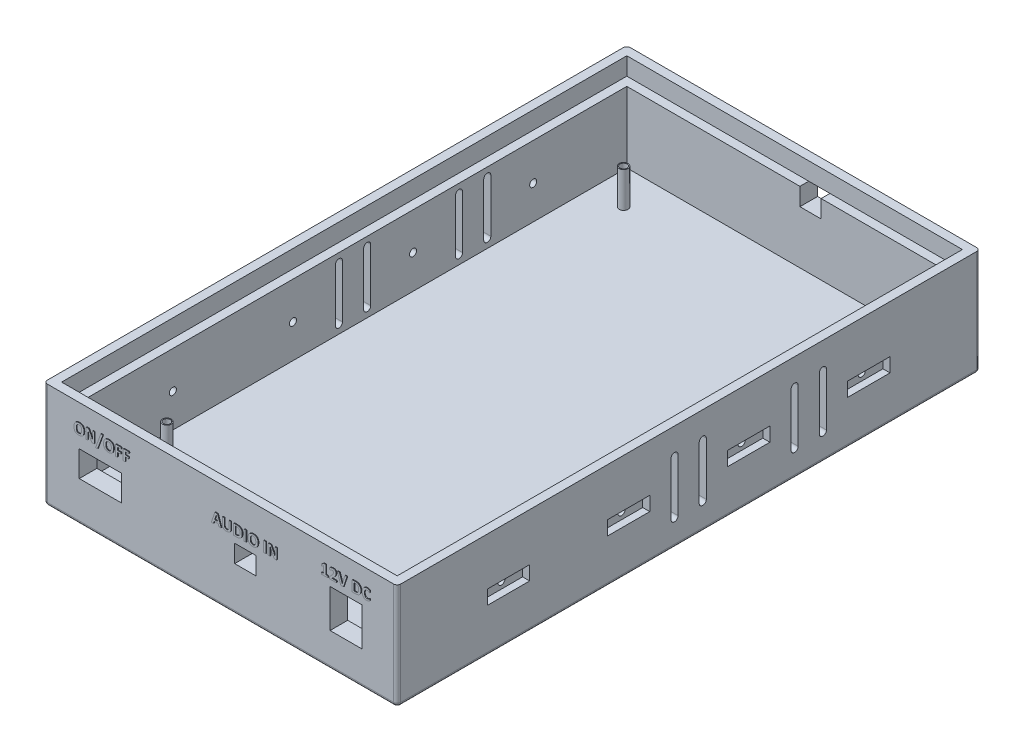
SolidWorks part; units mm, degrees
ref_plane "Front Plane" through (0, 0, 0) normal (0, 0, 1) x (1, 0, 0)
ref_plane "Top Plane" through (0, 0, 0) normal (0, 1, 0) x (1, 0, 0)
ref_plane "Right Plane" through (0, 0, 0) normal (1, 0, 0) x (0, 0, -1)
sketch "Sketch1" plane through (0, 0, 0) normal (0, 1, 0) x (1, 0, 0)
  line L1 (0, 0) -> (100, 0)
  line L2 (0, 0) -> (0, 165)
  line L3 (0, 165) -> (100, 165)
  line L4 (100, 0) -> (100, 165)
  dimension "D1" = 100
  dimension "D2" = 165
extrude "Boss-Extrude1" add sketch "Sketch1" along normal blind 30
sketch "Sketch2" plane through (0, 30, 0) normal (0, 1, 0) x (1, 0, 0)
  line L8 (5, 160) -> (5, 5)
  line L9 (5, 5) -> (95, 5)
  line L10 (95, 5) -> (95, 160)
  line L11 (95, 160) -> (5, 160)
  line L12 (5, 160) -> (5, 5)
  line L13 (5, 5) -> (95, 5)
  line L14 (95, 5) -> (95, 160)
  line L15 (95, 160) -> (5, 160)
  dimension "D1" = 5
extrude "Cut-Extrude1" cut sketch "Sketch2" against normal offset from surface (25 mm away) 5 up to face at (50, 0, -82.5)
sketch "Sketch3" plane through (0, 0, 0) normal (-1, 0, 0) x (0, 0, 1)
  line L1 (-126.3853, 10.954) -> (-116.3853, 10.954)
  line L2 (-126.3853, 10.954) -> (-126.3853, 5.954)
  line L3 (-126.3853, 5.954) -> (-116.3853, 5.954)
  line L4 (-116.3853, 10.954) -> (-116.3853, 5.954)
  dimension "D1" = 10
  dimension "D2" = 5
extrude "Boss-Extrude2" add sketch "Sketch3" along normal blind 15 separate body
sketch "Sketch4" plane through (0, 5.954, 0) normal (0, -1, 0) x (1, 0, 0)
  line L0 (-15, -116.3853) -> (0, -116.3853) construction
  line L1 (-15, -126.3853) -> (-10, -126.3853)
  line L2 (-15, -126.3853) -> (-15, -116.3853)
  line L3 (-15, -116.3853) -> (-10, -116.3853)
  line L4 (-10, -126.3853) -> (-10, -116.3853)
  dimension "D1" = 5
extrude "Boss-Extrude3" add sketch "Sketch4" along normal blind 20
chamfer "Chamfer1" distance 5 angle 45 1 edges at (-15, 10.954, -121.3853)
delete or keep bodies "Body-Delete/Keep 1" type delete bodies bodies 104
ref_plane "Plane1" through (50, 0, 0) normal (-1, 0, 0) x (0, 0, 1)
sketch "Sketch7" plane through (0, 0, 0) normal (-1, 0, 0) x (0, 0, 1)
  line L0 (-165, 30) -> (-165, 0) construction
  line L1 (-139.5, 16.5) -> (-127.5, 16.5)
  line L2 (-139.5, 16.5) -> (-139.5, 12.5)
  line L3 (-139.5, 12.5) -> (-127.5, 12.5)
  line L4 (-127.5, 16.5) -> (-127.5, 12.5)
  line L6 (-105.5, 16.5) -> (-105.5, 12.5)
  line L7 (-105.5, 16.5) -> (-93.5, 16.5)
  line L8 (-93.5, 16.5) -> (-93.5, 12.5)
  line L9 (-105.5, 12.5) -> (-93.5, 12.5)
  line L10 (-71.5, 16.5) -> (-71.5, 12.5)
  line L11 (-71.5, 16.5) -> (-59.5, 16.5)
  line L12 (-59.5, 16.5) -> (-59.5, 12.5)
  line L13 (-71.5, 12.5) -> (-59.5, 12.5)
  line L14 (-37.5, 16.5) -> (-37.5, 12.5)
  line L15 (-37.5, 16.5) -> (-25.5, 16.5)
  line L16 (-25.5, 16.5) -> (-25.5, 12.5)
  line L17 (-37.5, 12.5) -> (-25.5, 12.5)
  line L18 (0, 30) -> (0, 0) construction
  line L19 (-165, 0) -> (0, 0) construction
  dimension "D1" = 12
  dimension "D2" = 4
  dimension "D3" = 25.5
  dimension "D4" = 12.5
  dimension "D6" = 22
  dimension "D7" = 25.5
  dimension "D5" = 4
extrude "Cut-Extrude2" cut sketch "Sketch7" against normal blind 2
mirror "Mirror1" about plane through (50, 0, 0) normal (-1, 0, 0) of "Cut-Extrude2"
sketch "Sketch8" plane through (2, 0, 0) normal (-1, 0, 0) x (0, 0, 1)
  line L0 (-127.5, 12.5) -> (-127.5, 16.5) construction
  line L1 (-165, 30) -> (-165, 0) construction
  line L2 (-127.5, 16.5) -> (-139.5, 16.5) construction
  line L3 (0, 30) -> (0, 0) construction
  circle A0 centre (-133.5, 14.5) radius 1
  circle A1 centre (-99.5, 14.5) radius 1
  circle A2 centre (-65.5, 14.5) radius 1
  circle A3 centre (-31.5, 14.5) radius 1
  point P11 (-127.5, 14.5)
  point P17 (-133.5, 16.5)
  dimension "D1" = 2
  dimension "D2" = 2
  dimension "D3" = 2
  dimension "D4" = 2
  dimension "D5" = 34
  dimension "D8" = 31.5
  dimension "D9" = 31.5
  dimension "D6" = 34
  dimension "D7" = 34
extrude "Cut-Extrude3" cut sketch "Sketch8" against normal through all both and the other way through all
sketch "Sketch10" plane through (0, 0, 0) normal (0, 0, 1) x (1, 0, 0)
  line L0 (0, 30) -> (0, 0) construction
  line L1 (10, 18.65) -> (22, 18.65)
  line L2 (10, 18.65) -> (10, 11.35)
  line L3 (10, 11.35) -> (22, 11.35)
  line L4 (22, 18.65) -> (22, 11.35)
  point P4 (10, 15)
  point P7 (0, 15)
  dimension "D1" = 12
  dimension "D2" = 7.3
  dimension "D3" = 10
extrude "Cut-Extrude4" cut sketch "Sketch10" against normal up to surface (5 mm away) up to face at (50, 17.5, -5)
sketch "Sketch11" plane through (0, 0, 0) normal (0, 0, 1) x (1, 0, 0)
  line L0 (100, 30) -> (100, 0) construction
  line L5 (54, 17.5) -> (60, 17.5)
  line L6 (54, 17.5) -> (54, 12.5)
  line L7 (54, 12.5) -> (60, 12.5)
  line L8 (60, 17.5) -> (60, 12.5)
  point P4 (54, 15)
  point P7 (100, 15)
  dimension "D1" = 6
  dimension "D2" = 5
  dimension "D3" = 40
extrude "Cut-Extrude5" cut sketch "Sketch11" against normal up to surface (5 mm away) up to face at (16, 15, -5)
sketch "Sketch12" plane through (0, 0, 0) normal (0, 0, 1) x (1, 0, 0)
  line L0 (100, 30) -> (100, 0) construction
  line L1 (81, 20.4) -> (90, 20.4)
  line L2 (81, 20.4) -> (81, 9.6)
  line L3 (81, 9.6) -> (90, 9.6)
  line L4 (90, 20.4) -> (90, 9.6)
  point P4 (90, 15)
  point P7 (100, 15)
  dimension "D1" = 10.8
  dimension "D2" = 9
  dimension "D3" = 10
extrude "Cut-Extrude6" cut sketch "Sketch12" against normal up to surface (5 mm away) up to face at (57, 15, -5)
sketch "Sketch13" plane through (0, 0, -165) normal (0, 0, -1) x (-1, 0, 0)
  line L0 (-100, 30) -> (-100, 0) construction
  line L1 (-60, 25) -> (-54, 25)
  line L2 (-60, 25) -> (-60, 20)
  line L3 (-60, 20) -> (-54, 20)
  line L4 (-54, 25) -> (-54, 20)
  line L5 (-100, 30) -> (0, 30) construction
  dimension "D1" = 6
  dimension "D2" = 5
  dimension "D3" = 40
  dimension "D4" = 5
extrude "Cut-Extrude7" cut sketch "Sketch13" against normal up to surface (5 mm away) up to face at (50, 17.5, -160)
sketch "Sketch14" plane through (0, 5, 0) normal (0, 1, 0) x (1, 0, 0)
  circle A0 centre (12.085, 22.713) radius 1.25
  circle A1 centre (86, 22.713) radius 1.25
  circle A2 centre (86, 150) radius 1.25
  circle A3 centre (14.085, 150) radius 1.25
  circle A4 centre (14.085, 150) radius 1
  circle A5 centre (12.085, 22.713) radius 1
  circle A6 centre (86, 22.713) radius 1
  circle A7 centre (86, 150) radius 1
  dimension "D1" = 2
  dimension "D2" = 2
  dimension "D3" = 2
  dimension "D4" = 2
extrude "Boss-Extrude4" add sketch "Sketch14" along normal blind 10
sketch "Sketch15" plane through (0, 30, 0) normal (0, 1, 0) x (1, 0, 0)
  line L14 (5, 5) -> (95, 5)
  line L15 (5, 160) -> (5, 5)
  line L16 (95, 160) -> (5, 160)
  line L17 (95, 5) -> (95, 160)
  line L18 (5, 5) -> (95, 5)
  line L19 (5, 160) -> (5, 5)
  line L20 (95, 160) -> (5, 160)
  line L21 (95, 5) -> (95, 160)
  line L26 (97.5, 162.5) -> (2.5, 162.5)
  line L27 (2.5, 162.5) -> (2.5, 2.5)
  line L28 (2.5, 2.5) -> (97.5, 2.5)
  line L29 (97.5, 2.5) -> (97.5, 162.5)
  line L30 (97.5, 162.5) -> (2.5, 162.5)
  line L31 (2.5, 162.5) -> (2.5, 2.5)
  line L32 (2.5, 2.5) -> (97.5, 2.5)
  line L33 (97.5, 2.5) -> (97.5, 162.5)
  dimension "D1" = 0
  dimension "D2" = 2.5
extrude "Cut-Extrude8" cut sketch "Sketch15" against normal blind 5
sketch "Sketch16" plane through (0, 0, 0) normal (-1, 0, 0) x (0, 0, 1)
  line L2 (-121.5, 22.5) -> (-121.5, 7.5)
  line L4 (-119.5, 22.5) -> (-119.5, 7.5)
  line L6 (-113.5, 22.5) -> (-113.5, 7.5)
  line L8 (-111.5, 22.5) -> (-111.5, 7.5)
  line L10 (-87.5, 22.5) -> (-87.5, 7.5)
  line L12 (-85.5, 22.5) -> (-85.5, 7.5)
  line L14 (-79.5, 22.5) -> (-79.5, 7.5)
  line L16 (-77.5, 22.5) -> (-77.5, 7.5)
  line L17 (-127.5, 12.5) -> (-127.5, 16.5) construction
  line L18 (-105.5, 14.5) -> (-105.5, -11.4289) construction
  line L19 (-93.5, 12.5) -> (-93.5, 16.5) construction
  arc A0 (-119.5, 22.5) -> (-121.5, 22.5) centre (-120.5, 22.5) ccw
  arc A1 (-111.5, 22.5) -> (-113.5, 22.5) centre (-112.5, 22.5) ccw
  arc A2 (-121.5, 7.5) -> (-119.5, 7.5) centre (-120.5, 7.5) ccw
  arc A3 (-113.5, 7.5) -> (-111.5, 7.5) centre (-112.5, 7.5) ccw
  arc A4 (-87.5, 7.5) -> (-85.5, 7.5) centre (-86.5, 7.5) ccw
  arc A5 (-79.5, 7.5) -> (-77.5, 7.5) centre (-78.5, 7.5) ccw
  arc A6 (-85.5, 22.5) -> (-87.5, 22.5) centre (-86.5, 22.5) ccw
  arc A7 (-77.5, 22.5) -> (-79.5, 22.5) centre (-78.5, 22.5) ccw
  point P22 (-120.5, 23.5)
  point P23 (-112.5, 23.5)
  point P24 (-86.5, 23.5)
  point P25 (-78.5, 23.5)
  point P26 (-120.5, 6.5)
  point P28 (-112.5, 6.5)
  point P30 (-86.5, 6.5)
  point P32 (-78.5, 6.5)
  dimension "D1" = 2
  dimension "D2" = 2
  dimension "D3" = 2
  dimension "D4" = 2
  dimension "D5" = 6
  dimension "D6" = 6
  dimension "D7" = 6
  dimension "D8" = 6
  dimension "D9" = 6
  dimension "D10" = 15
extrude "Cut-Extrude9" cut sketch "Sketch16" against normal blind 5
mirror "Mirror2" about plane through (50, 0, 0) normal (-1, 0, 0) of "Cut-Extrude9"
fillet "Fillet1" radius 1 8 edges at (50, 0, 0) (100, 0, -82.5) (50, 0, -165) (0, 0, -82.5) (100, 15, 0) (100, 15, -165) (0, 15, -165) (0, 15, 0)
sketch "Sketch17" plane through (0, 0, 0) normal (0, 0, 1) x (1, 0, 0)
  line L0 (8.5158, 22.15) -> (23.4842, 22.15) construction
  line L1 (23.5, 20.15) -> (8.5, 20.15) construction
  line L2 (45.3641, 19.5) -> (68.6359, 19.5) construction
  line L3 (60, 17.5) -> (54, 17.5) construction
  line L4 (22, 18.65) -> (10, 18.65) construction
  line L5 (76.1212, 22.4) -> (94.8788, 22.4) construction
  line L6 (90, 20.4) -> (81, 20.4) construction
  text T0 "ON/OFF" font "Calibri" height 3
  text T1 "AUDIO IN" font "Calibri" height 3
  text T2 "12V DC" font "Calibri" height 3
  point P10 (16, 22.15)
  point P11 (57, 17.5)
  point P12 (57, 19.5)
  point P15 (16, 18.65)
  point P19 (85.5, 20.4)
  point P20 (85.5, 22.4)
  point P22 (45.3641, 19.5)
  dimension "D1" = 2
  dimension "D2" = 2
  dimension "D3" = 2
extrude "Boss-Extrude5" add sketch "Sketch17" along normal blind 0.2 separate body
sketch "Sketch18" plane through (0, 0, -165) normal (0, 0, -1) x (-1, 0, 0)
  line L0 (-73.2212, 15) -> (-40.7788, 15) construction
  line L1 (-60, 20) -> (-54, 20) construction
  text T0 "AUDIO OUT" font "Calibri" height 3
  point P5 (-39.6777, 15)
  point P6 (-57, 20)
  point P7 (-57, 15)
  point P8 (-73.2212, 15)
  dimension "D1" = 5
extrude "Boss-Extrude6" add sketch "Sketch18" along normal blind 0.2 separate body
